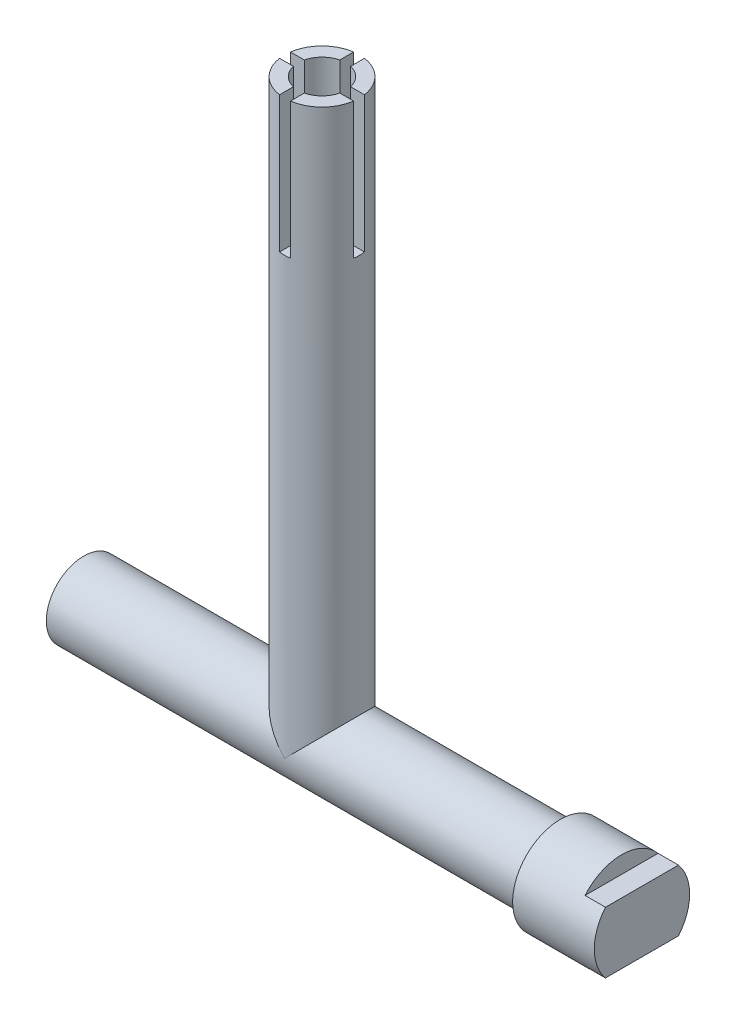
SolidWorks part; units mm, degrees
material "Сталь"
ref_plane "Спереди" through (0, 0, 0) normal (0, 0, 1) x (1, 0, 0)
ref_plane "Сверху" through (0, 0, 0) normal (0, 1, 0) x (1, 0, 0)
ref_plane "Справа" through (0, 0, 0) normal (1, 0, 0) x (0, 0, -1)
sketch "Эскиз1" plane through (0, 0, 0) normal (1, 0, 0) x (0, 0, -1)
  circle A0 centre (0, 0) radius 2.75
  dimension "D1" = 5.5
extrude "Бобышка-Вытянуть1" add sketch "Эскиз1" along normal blind 35
sketch "Эскиз2" plane through (0, 0, 0) normal (0, 1, 0) x (1, 0, 0)
  line L0 (0, 0) -> (35, 0) construction
  line L1 (35, -2.75) -> (35, 2.75) construction
  circle A0 centre (17.5, 0) radius 2.75
  dimension "D1" = 5.5
extrude "Бобышка-Вытянуть2" add sketch "Эскиз2" along normal blind 42
hole_wizard "Диаметр отверстия Ø3.5 (3.5)1" positions "Трехмерный эскиз1" profile "Эскиз3" hole size "Ø3.5" standard "Ansi Metric"
sketch3d "Трехмерный эскиз1"
  line L0 (17.5, 42, 0) -> (17.5, 0, 0) construction
  point P0 (17.5, 42, 0)
sketch "Эскиз3" plane through (17.5, 42, 0) normal (1, 0, 0) x (0, 0, 1)
  line L0 (0, 0) -> (0, 14.0515)
  line L1 (0, 14.0515) -> (1.75, 13)
  line L2 (1.75, 13) -> (1.75, 0)
  line L5 (1.75, 0) -> (0, 0)
  line L10 (0, 14.0515) -> (-1.75, 13) construction
  line L11 (0, -6.35) -> (0, 107.95) construction
  dimension "Диаметр отверстия" = 3.5
  dimension "Глубина отверстия" = 13
  dimension "Угол заточки сверла" = 118
sketch "Эскиз4" plane through (0, 42, 0) normal (0, 1, 0) x (1, 0, 0)
  line L1 (17.1, -4) -> (17.9, -4)
  line L2 (17.1, -4) -> (17.1, 4)
  line L3 (17.1, 4) -> (17.9, 4)
  line L4 (17.9, -4) -> (17.9, 4)
  line L5 (17.1, -4) -> (17.9, 4) construction
  line L6 (17.1, 4) -> (17.9, -4) construction
  line L7 (13.5, -0.4) -> (21.5, -0.4)
  line L8 (13.5, -0.4) -> (13.5, 0.4)
  line L9 (13.5, 0.4) -> (21.5, 0.4)
  line L10 (21.5, -0.4) -> (21.5, 0.4)
  line L11 (13.5, -0.4) -> (21.5, 0.4) construction
  line L12 (13.5, 0.4) -> (21.5, -0.4) construction
  point P0 (17.5, 0)
  point P6 (17.5, 0)
  circle M1 centre (17.5, 0) radius 1.75
  circle M2 centre (17.5, 0) radius 2.75
  dimension "D1" = 0.8
  dimension "D2" = 8
extrude "Вырез-Вытянуть1" cut sketch "Эскиз4" against normal blind 10 contours L4 L3 L2 M2 | L4 L2 M1 M2 | L2 L9 L4 M1 | L9 L2 L7 L4 | L9 L7 L2 M1 | L9 L7 M2 M1 | L9 L8 L7 M2 | L4 L2 M2 M1 | L7 L2 L4 M1 | L1 L4 L2 M2 | L9 L4 L7 M1 | L9 L7 M1 M2 | L7 L10 L9 M2
sketch "Эскиз5" plane through (35, 0, 0) normal (1, 0, 0) x (0, 0, -1)
  circle A0 centre (0, 0) radius 3.5
  dimension "D1" = 7
extrude "Бобышка-Вытянуть3" add sketch "Эскиз5" along normal blind 6
sketch "Эскиз6" plane through (41, 0, 0) normal (1, 0, 0) x (0, 0, -1)
  line L1 (-2.681, -2.25) -> (2.681, -2.25)
  line L2 (-2.681, -2.25) -> (-2.681, 2.25)
  line L3 (-2.681, 2.25) -> (2.681, 2.25)
  line L4 (2.681, -2.25) -> (2.681, 2.25)
  line L5 (-2.681, -2.25) -> (2.681, 2.25) construction
  line L6 (-2.681, 2.25) -> (2.681, -2.25) construction
  circle A0 centre (0, 0) radius 3.5 construction
  circle A1 centre (0, 0) radius 3.5
  circle M1 centre (0, 0) radius 3.5
  dimension "D1" = 4.5
extrude "Вырез-Вытянуть2" cut sketch "Эскиз6" against normal blind 1.5 contours L3 M1 | L1 M1
sketch "Эскиз7" plane through (0, 0, 0) normal (-1, 0, 0) x (0, 0, 1)
  circle A0 centre (0, 0) radius 2
  dimension "D1" = 4
extrude "Вырез-Вытянуть3" cut sketch "Эскиз7" against normal blind 7
hole_wizard "Отверстие обработанное метчиком M2.5x0.451" positions "Трехмерный эскиз2" profile "Эскиз8" tap size "M2.5x0.45" standard "Ansi Metric"
sketch3d "Трехмерный эскиз2"
  line L0 (7, 0, 0) -> (0, 0, 0) construction
  point P0 (7, 0, 0)
sketch "Эскиз8" plane through (7, 0, 0) normal (0, 1, 0) x (0, 0, 1)
  line L0 (0, 0) -> (0, 6.6159)
  line L1 (0, 6.6159) -> (1.025, 6)
  line L2 (1.025, 6) -> (1.025, 0)
  line L5 (1.025, 0) -> (0, 0)
  line L10 (0, 6.6159) -> (-1.025, 6) construction
  line L11 (0, -6.35) -> (0, 107.95) construction
  dimension "Диаметр сверла" = 2.05
  dimension "Глубина сверла" = 6
  dimension "Угол заточки сверла" = 118
cosmetic thread "Отверстие резьбы1" parameters "D1"=4.5, "D2"=2.5
